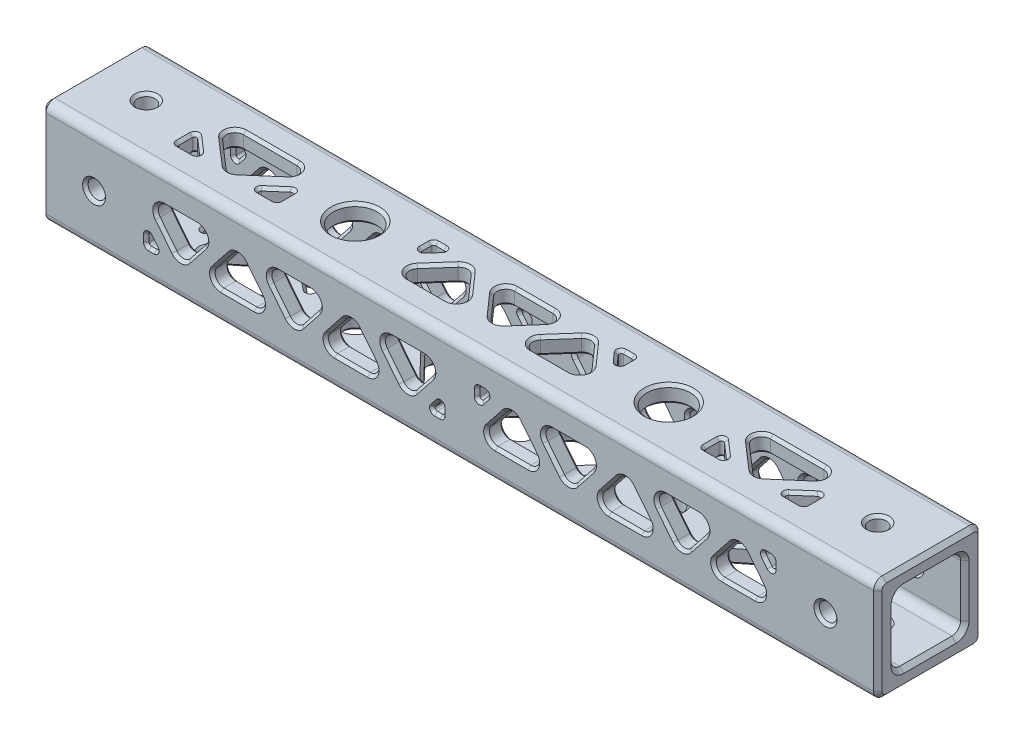
SolidWorks part; units mm, degrees
ref_plane "Front Plane" through (0, 0, 0) normal (0, 0, 1) x (1, 0, 0)
ref_plane "Top Plane" through (0, 0, 0) normal (0, 1, 0) x (1, 0, 0)
ref_plane "Right Plane" through (0, 0, 0) normal (1, 0, 0) x (0, 0, -1)
sketch "Sketch1" plane through (0, 0, 0) normal (1, 0, 0) x (0, 0, -1)
  line L1 (-6.35, -6.35) -> (6.35, -6.35)
  line L2 (-6.35, -6.35) -> (-6.35, 6.35)
  line L3 (-6.35, 6.35) -> (6.35, 6.35)
  line L4 (6.35, -6.35) -> (6.35, 6.35)
  line L5 (-6.35, -6.35) -> (6.35, 6.35) construction
  line L6 (-6.35, 6.35) -> (6.35, -6.35) construction
  line L7 (-9.525, -9.525) -> (9.525, -9.525)
  line L8 (-9.525, -9.525) -> (-9.525, 9.525)
  line L9 (-9.525, 9.525) -> (9.525, 9.525)
  line L10 (9.525, -9.525) -> (9.525, 9.525)
  line L11 (-9.525, -9.525) -> (9.525, 9.525) construction
  line L12 (-9.525, 9.525) -> (9.525, -9.525) construction
  point P0 (0, 0)
  point P6 (0, 0)
  dimension "D1" = 19.05
  dimension "D2" = 12.7
extrude "Boss-Extrude1" add sketch "Sketch1" along normal mid plane 152.4 contours L9 L10 L7 L8
hole_wizard "1/8 (0.125) Diameter Hole1" positions "Sketch2" profile "Sketch3" hole size "1/8" standard "ANSI Inch" end condition through all
sketch "Sketch2" plane through (0, 0, 9.525) normal (0, 0, 1) x (1, 0, 0)
  line L0 (-76.2, 0) -> (-66.675, 0) construction
  line L1 (-76.2, 9.525) -> (-76.2, -9.525) construction
  line L2 (-66.675, 0) -> (66.675, 0) construction
  line L3 (66.675, 0) -> (76.2, 0) construction
  line L4 (76.2, 9.525) -> (76.2, -9.525) construction
  point P35 (-66.675, 0)
  point P37 (66.675, 0)
  dimension "D1" = 9.525
sketch "Sketch3" plane through (-66.675, 0, 9.525) normal (1, 0, 0) x (0, -1, 0)
  line L0 (0, 0) -> (0, 19.05)
  line L1 (0, 19.05) -> (1.5875, 19.05)
  line L2 (1.5875, 19.05) -> (1.5875, 0)
  line L5 (1.5875, 0) -> (0, 0)
  line L11 (0, -6.35) -> (0, 107.95) construction
  dimension "Thru Hole Dia." = 3.175
  dimension "Thru Hole Depth" = 19.05
hole_wizard "1/8 (0.125) Diameter Hole2" positions "Sketch4" profile "Sketch5" hole size "1/8" standard "ANSI Inch" end condition through all
sketch "Sketch4" plane through (0, 9.525, 0) normal (0, 1, 0) x (1, 0, 0)
  line L0 (-76.2, 0) -> (-66.675, 0) construction
  line L1 (-76.2, 9.525) -> (-76.2, -9.525) construction
  line L2 (-66.675, 0) -> (66.675, 0) construction
  line L3 (66.675, 0) -> (76.2, 0) construction
  line L4 (76.2, 9.525) -> (76.2, -9.525) construction
  point P27 (-66.675, 0)
  point P29 (66.675, 0)
  dimension "D1" = 9.525
sketch "Sketch5" plane through (-66.675, 9.525, 0) normal (1, 0, 0) x (0, 0, 1)
  line L0 (0, 0) -> (0, 19.05)
  line L1 (0, 19.05) -> (1.5875, 19.05)
  line L2 (1.5875, 19.05) -> (1.5875, 0)
  line L5 (1.5875, 0) -> (0, 0)
  line L11 (0, -6.35) -> (0, 107.95) construction
  dimension "Thru Hole Dia." = 3.175
  dimension "Thru Hole Depth" = 19.05
hole_wizard "3/16 (0.1875) Diameter Hole1" positions "Sketch6" profile "Sketch7" hole size "3/16" standard "ANSI Inch" end condition up to next
sketch "Sketch6" plane through (0, -9.525, 0) normal (0, -1, 0) x (-1, 0, 0)
  line L0 (-28.575, 0) -> (28.575, 0) construction
  point P0 (28.575, 0)
  point P2 (-28.575, 0)
  dimension "D1" = 57.15
sketch "Sketch7" plane through (-28.575, -9.525, 0) normal (1, 0, 0) x (0, 0, -1)
  line L0 (0, 0) -> (0, 3.175)
  line L1 (0, 3.175) -> (2.3812, 3.175)
  line L2 (2.3812, 3.175) -> (2.3812, 0)
  line L5 (2.3812, 0) -> (0, 0)
  line L11 (0, -6.35) -> (0, 107.95) construction
  dimension "Thru Hole Dia." = 4.7625
  dimension "Thru Hole Depth" = 3.175
sketch "Sketch10" plane through (0, 9.525, 0) normal (0, 1, 0) x (1, 0, 0)
  line L0 (28.575, 0) -> (-28.575, 0) construction
  circle A0 centre (-28.575, 0) radius 3.9688
  circle A1 centre (28.575, 0) radius 3.9687
  circle A3 centre (28.575, 0) radius 2.3812 construction
  dimension "D1" = 7.9375
extrude "Cut-Extrude3" cut sketch "Sketch10" against normal up to next
ref_axis "Axis1" through (-82.0738, 0, 0) along (1, 0, 0)
sketch "Sketch9" plane through (0, -9.525, 0) normal (0, -1, 0) x (1, 0, 0)
  line L0 (-57.15, 9.525) -> (-57.15, -9.525) construction
  line L1 (76.2, 9.525) -> (-76.2, 9.525) construction
  line L2 (76.2, -9.525) -> (-76.2, -9.525) construction
  line L3 (57.15, 9.525) -> (57.15, -9.525) construction
  line L4 (-76.2, 9.525) -> (-76.2, -9.525) construction
  line L5 (-28.575, 0) -> (-28.575, -9.525) construction
  line L6 (-28.575, 0) -> (-28.575, 9.525) construction
  line L7 (-30.9562, 0) -> (-30.9563, -9.525) construction
  line L8 (-30.9562, 0) -> (-30.9563, 9.525) construction
  line L9 (-37.3062, 9.525) -> (-37.3062, -9.525) construction
  line L10 (-26.1938, 0) -> (-26.1938, -9.525) construction
  line L11 (-26.1938, 0) -> (-26.1938, 9.525) construction
  line L12 (-19.8438, 9.525) -> (-19.8438, -9.525) construction
  line L13 (-30.9562, 0) -> (-37.3062, 0) construction
  line L14 (-26.1938, 0) -> (-19.8438, 0) construction
  line L15 (28.575, 0) -> (28.575, 9.525) construction
  line L16 (28.575, 0) -> (28.575, -9.525) construction
  line L17 (30.9562, 0) -> (30.9562, -9.525) construction
  line L18 (30.9562, 0) -> (30.9562, 9.525) construction
  line L19 (26.1938, 0) -> (26.1938, -9.525) construction
  line L20 (26.1938, 0) -> (26.1938, 9.525) construction
  line L21 (19.8438, 9.525) -> (19.8438, -9.525) construction
  line L22 (19.8438, 0) -> (26.1938, 0) construction
  line L23 (37.3062, 9.525) -> (37.3062, -9.525) construction
  line L24 (30.9562, 0) -> (37.3062, 0) construction
  line L25 (57.15, 0) -> (76.2, 0) construction
  line L26 (76.2, 9.525) -> (76.2, -9.525) construction
  line L27 (-57.15, 0) -> (-76.2, 0) construction
  line L28 (-57.15, 3.9688) -> (-37.3062, 3.9688) construction
  line L29 (-57.15, -3.9688) -> (-37.3062, -3.9688) construction
  line L30 (-47.2281, -9.525) -> (-47.2281, -3.9688) construction
  line L31 (-47.2281, 3.9688) -> (-47.2281, 9.525) construction
  line L32 (-19.8438, 3.9688) -> (19.8438, 3.9688) construction
  line L33 (-19.8438, -3.9688) -> (19.8438, -3.9688) construction
  line L34 (37.3062, 3.9688) -> (57.15, 3.9688) construction
  line L35 (37.3062, -3.9688) -> (57.15, -3.9688) construction
  line L36 (-19.8438, 3.9688) -> (-19.8438, 0.5884)
  line L37 (-19.8438, 0.5884) -> (-16.5608, 3.9688)
  line L38 (-16.5608, 3.9688) -> (-19.8438, 3.9688)
  line L39 (-19.8438, -3.9688) -> (-12.1348, 3.9688)
  line L40 (-12.1348, 3.9688) -> (-4.4259, -3.9688)
  line L41 (-4.4259, -3.9688) -> (-19.8438, -3.9688)
  line L42 (-18.2023, 2.2786) -> (-15.9246, 0.0666) construction
  line L43 (-7.7089, 3.9688) -> (0, -3.9688)
  line L44 (0, -3.9688) -> (7.7089, 3.9688)
  line L45 (7.7089, 3.9688) -> (-7.7089, 3.9688)
  line L46 (19.8438, -3.9688) -> (12.1348, 3.9688)
  line L47 (12.1348, 3.9688) -> (4.4259, -3.9688)
  line L48 (4.4259, -3.9688) -> (19.8438, -3.9688)
  line L49 (16.5608, 3.9688) -> (19.8438, 3.9688)
  line L50 (19.8438, 3.9688) -> (19.8438, 0.5884)
  line L51 (19.8438, 0.5884) -> (16.5608, 3.9688)
  line L52 (-3.8545, 0) -> (-6.1321, -2.212) construction
  line L53 (3.8545, 0) -> (6.1321, -2.212) construction
  line L54 (18.2023, 2.2786) -> (15.9246, 0.0666) construction
  line L55 (-37.3062, -3.9688) -> (-37.3062, -0.0972)
  line L56 (-37.3062, -0.0972) -> (-42.1456, -3.9688)
  line L57 (-42.1456, -3.9688) -> (-37.3062, -3.9688)
  line L58 (-57.15, -3.9688) -> (-57.15, -0.0972)
  line L59 (-57.15, -0.0972) -> (-52.3106, -3.9688)
  line L60 (-52.3106, -3.9688) -> (-57.15, -3.9688)
  line L61 (-57.15, 3.9688) -> (-47.2281, -3.9688)
  line L62 (-47.2281, -3.9688) -> (-37.3062, 3.9688)
  line L63 (-37.3062, 3.9688) -> (-57.15, 3.9688)
  line L64 (-54.7303, -2.033) -> (-52.7469, 0.4463) construction
  line L65 (-39.7259, -2.033) -> (-41.7094, 0.4463) construction
  line L66 (37.3062, -0.0972) -> (37.3062, -3.9688)
  line L67 (37.3062, -3.9688) -> (42.1456, -3.9688)
  line L68 (42.1456, -3.9688) -> (37.3062, -0.0972)
  line L69 (52.3106, -3.9688) -> (57.15, -3.9688)
  line L70 (57.15, -3.9688) -> (57.15, -0.0972)
  line L71 (57.15, -0.0972) -> (52.3106, -3.9688)
  line L72 (37.3062, 3.9688) -> (47.2281, -3.9688)
  line L73 (47.2281, -3.9688) -> (57.15, 3.9688)
  line L74 (57.15, 3.9688) -> (37.3062, 3.9688)
  line L75 (39.7259, -2.033) -> (41.7094, 0.4463) construction
  line L76 (54.7303, -2.033) -> (52.7469, 0.4463) construction
  circle A0 centre (-28.575, 0) radius 2.3812 construction
  circle A1 centre (28.575, 0) radius 2.3812 construction
  dimension "D1" = 19.05
  dimension "D2" = 6.35
  dimension "D3" = 7.9375
  dimension "D4" = 3.175
extrude "Cut-Extrude2" cut sketch "Sketch9" against normal up to next contours L62 L63 L61
sketch "Sketch11" plane through (0, 9.525, 0) normal (0, 1, 0) x (1, 0, 0)
  line L0 (-57.15, 9.525) -> (-57.15, -9.525) construction
  line L1 (76.2, 9.525) -> (-76.2, 9.525) construction
  line L2 (76.2, -9.525) -> (-76.2, -9.525) construction
  line L3 (-76.2, 9.525) -> (-76.2, -9.525) construction
  line L4 (57.15, 9.525) -> (57.15, -9.525) construction
  line L5 (57.15, 0) -> (76.2, 0) construction
  line L6 (76.2, 9.525) -> (76.2, -9.525) construction
  line L7 (-57.15, 0) -> (-76.2, 0) construction
  line L8 (-28.575, 0) -> (-28.575, -9.525) construction
  line L9 (-28.575, 0) -> (-28.575, 9.525) construction
  line L10 (28.575, 0) -> (28.575, -9.525) construction
  line L11 (28.575, 0) -> (28.575, 9.525) construction
  line L12 (-32.5437, 0) -> (-32.5437, 9.525) construction
  line L13 (-32.5437, 0) -> (-32.5437, -9.525) construction
  line L14 (-24.6062, 0) -> (-24.6062, 9.525) construction
  line L15 (-24.6062, 0) -> (-24.6062, -9.525) construction
  line L16 (24.6062, 0) -> (24.6062, 9.525) construction
  line L17 (24.6062, 0) -> (24.6062, -9.525) construction
  line L18 (32.5437, 0) -> (32.5437, 9.525) construction
  line L19 (32.5437, 0) -> (32.5437, -9.525) construction
  line L20 (-38.8938, 9.525) -> (-38.8938, -9.525) construction
  line L21 (-18.2562, 9.525) -> (-18.2563, -9.525) construction
  line L22 (18.2562, 9.525) -> (18.2563, -9.525) construction
  line L23 (38.8938, 9.525) -> (38.8938, -9.525) construction
  line L24 (-32.5437, 0) -> (-38.8938, 0) construction
  line L25 (-24.6062, 0) -> (-18.2562, 0) construction
  line L26 (24.6062, 0) -> (18.2562, 0) construction
  line L27 (32.5437, 0) -> (38.8937, 0) construction
  line L28 (-57.15, 3.9688) -> (-38.8938, 3.9688) construction
  line L29 (-18.2562, 3.9688) -> (18.2562, 3.9688) construction
  line L30 (38.8937, 3.9688) -> (57.15, 3.9688) construction
  line L31 (57.15, -3.9688) -> (38.8937, -3.9688) construction
  line L32 (18.2562, -3.9688) -> (-18.2562, -3.9688) construction
  line L33 (-38.8938, -3.9688) -> (-57.15, -3.9688) construction
  line L34 (0, -3.9687) -> (0, -9.525) construction
  line L35 (0, 3.9687) -> (0, 9.525) construction
  line L36 (-57.15, -3.9688) -> (-57.15, -0.2387)
  line L37 (-57.15, -0.2387) -> (-52.8605, -3.9688)
  line L38 (-52.8605, -3.9688) -> (-57.15, -3.9688)
  line L39 (-57.15, 3.9688) -> (-48.0219, -3.9688)
  line L40 (-48.0219, -3.9688) -> (-38.8938, 3.9688)
  line L41 (-38.8938, 3.9688) -> (-57.15, 3.9688)
  line L42 (-43.1833, -3.9688) -> (-38.8938, -3.9688)
  line L43 (-38.8938, -3.9688) -> (-38.8938, -0.2387)
  line L44 (-38.8938, -0.2387) -> (-43.1833, -3.9688)
  line L45 (-55.0052, -2.1037) -> (-52.9219, 0.2921) construction
  line L46 (-41.0385, -2.1037) -> (-43.1219, 0.2921) construction
  line L47 (-18.2562, 3.9688) -> (-18.2562, 0.8276)
  line L48 (-18.2562, 0.8276) -> (-15.4821, 3.9688)
  line L49 (-15.4821, 3.9688) -> (-18.2562, 3.9688)
  line L50 (15.4821, 3.9688) -> (18.2562, 3.9688)
  line L51 (18.2562, 3.9688) -> (18.2562, 0.8276)
  line L52 (18.2562, 0.8276) -> (15.4821, 3.9688)
  line L53 (-18.2562, -3.9688) -> (-11.2461, 3.9688)
  line L54 (-11.2461, 3.9688) -> (-4.236, -3.9688)
  line L55 (-4.236, -3.9688) -> (-18.2562, -3.9688)
  line L56 (-7.0101, 3.9688) -> (0, -3.9687)
  line L57 (0, -3.9687) -> (7.0101, 3.9688)
  line L58 (7.0101, 3.9688) -> (-7.0101, 3.9688)
  line L59 (18.2562, -3.9688) -> (11.2461, 3.9688)
  line L60 (11.2461, 3.9688) -> (4.236, -3.9688)
  line L61 (4.236, -3.9688) -> (18.2562, -3.9688)
  line L62 (-16.8692, 2.3982) -> (-14.4894, 0.2964) construction
  line L63 (16.8692, 2.3982) -> (14.4894, 0.2964) construction
  line L64 (-3.5051, 0) -> (-5.8848, -2.1017) construction
  line L65 (3.5051, 0) -> (5.8848, -2.1017) construction
  line L66 (38.8937, -0.2387) -> (38.8937, -3.9688)
  line L67 (38.8937, -3.9688) -> (43.1833, -3.9688)
  line L68 (43.1833, -3.9688) -> (38.8937, -0.2387)
  line L69 (52.8605, -3.9688) -> (57.15, -3.9688)
  line L70 (57.15, -3.9688) -> (57.15, -0.2387)
  line L71 (57.15, -0.2387) -> (52.8605, -3.9688)
  line L72 (38.8937, 3.9688) -> (48.0219, -3.9688)
  line L73 (48.0219, -3.9688) -> (57.15, 3.9688)
  line L74 (57.15, 3.9688) -> (38.8937, 3.9688)
  line L75 (41.0385, -2.1037) -> (43.1219, 0.2921) construction
  line L76 (55.0052, -2.1037) -> (52.9219, 0.2921) construction
  circle A0 centre (-28.575, 0) radius 3.9688 construction
  circle A1 centre (28.575, 0) radius 3.9687 construction
  dimension "D1" = 19.05
  dimension "D2" = 6.35
  dimension "D3" = 7.9375
  dimension "D4" = 3.175
extrude "Cut-Extrude4" cut sketch "Sketch11" against normal up to next contours L39 L40 L41
sketch "Sketch13" plane through (0, 0, 9.525) normal (0, 0, 1) x (1, 0, 0)
  line L0 (-57.15, 9.525) -> (-57.15, -9.525) construction
  line L1 (76.2, 9.525) -> (-76.2, 9.525) construction
  line L2 (76.2, -9.525) -> (-76.2, -9.525) construction
  line L3 (57.15, 9.525) -> (57.15, -9.525) construction
  line L4 (-3.175, 9.525) -> (-3.175, -9.525) construction
  line L5 (3.175, 9.525) -> (3.175, -9.525) construction
  line L6 (-3.175, 0) -> (3.175, 0) construction
  line L7 (-57.15, 0) -> (-76.2, 0) construction
  line L9 (57.15, 0) -> (76.2, 0) construction
  line L10 (76.2, 9.525) -> (76.2, -9.525) construction
  line L11 (-57.15, 3.9688) -> (-3.175, 3.9688) construction
  line L12 (-57.15, -3.9688) -> (-3.175, -3.9688) construction
  line L13 (3.175, -3.9688) -> (57.15, -3.9688) construction
  line L14 (3.175, 3.9688) -> (57.15, 3.9688) construction
  line L15 (-30.1625, -3.9688) -> (-30.1625, -9.525) construction
  line L16 (-30.1625, 3.9688) -> (-30.1625, 9.525) construction
  line L17 (-57.15, -1.1411) -> (-57.15, -3.9688)
  line L18 (-57.15, -3.9688) -> (-54.9077, -3.9688)
  line L19 (-54.9077, -3.9688) -> (-57.15, -1.1411)
  line L20 (-3.175, -3.9688) -> (-3.175, -1.1411)
  line L21 (-3.175, -1.1411) -> (-5.4173, -3.9688)
  line L22 (-5.4173, -3.9688) -> (-3.175, -3.9688)
  line L23 (-30.1625, -3.9688) -> (-36.4569, 3.9688)
  line L24 (-36.4569, 3.9688) -> (-23.8681, 3.9688)
  line L25 (-23.8681, 3.9688) -> (-30.1625, -3.9688)
  line L26 (-57.15, 3.9688) -> (-50.8556, -3.9688)
  line L27 (-50.8556, -3.9688) -> (-44.5612, 3.9688)
  line L28 (-44.5612, 3.9688) -> (-57.15, 3.9688)
  line L29 (-3.175, 3.9688) -> (-9.4694, -3.9688)
  line L30 (-9.4694, -3.9688) -> (-15.7638, 3.9688)
  line L31 (-15.7638, 3.9688) -> (-3.175, 3.9688)
  line L32 (-46.8035, -3.9688) -> (-40.509, 3.9688)
  line L33 (-40.509, 3.9688) -> (-34.2146, -3.9688)
  line L34 (-34.2146, -3.9688) -> (-46.8035, -3.9688)
  line L35 (-26.1104, -3.9688) -> (-19.816, 3.9688)
  line L36 (-19.816, 3.9688) -> (-13.5215, -3.9688)
  line L37 (-13.5215, -3.9688) -> (-26.1104, -3.9688)
  line L38 (-56.0289, -2.5549) -> (-53.5411, -0.5822) construction
  line L39 (-47.7084, 0) -> (-45.2206, -1.9728) construction
  line L40 (-37.3618, 0) -> (-34.8741, 1.9728) construction
  line L41 (-22.9632, 0) -> (-25.4509, 1.9728) construction
  line L42 (-16.6687, 0) -> (-14.181, 1.9728) construction
  line L43 (-4.2961, -2.5549) -> (-6.7839, -0.5822) construction
  line L44 (3.175, 3.9688) -> (3.175, 1.1411)
  line L45 (3.175, 1.1411) -> (5.4173, 3.9688)
  line L46 (5.4173, 3.9688) -> (3.175, 3.9688)
  line L47 (57.15, 3.9688) -> (57.15, 1.1411)
  line L48 (57.15, 1.1411) -> (54.9077, 3.9688)
  line L49 (54.9077, 3.9688) -> (57.15, 3.9688)
  line L50 (23.8681, -3.9688) -> (30.1625, 3.9688)
  line L51 (30.1625, 3.9688) -> (36.4569, -3.9688)
  line L52 (36.4569, -3.9688) -> (23.8681, -3.9688)
  line L53 (3.175, -3.9688) -> (9.4694, 3.9688)
  line L54 (9.4694, 3.9688) -> (15.7638, -3.9688)
  line L55 (15.7638, -3.9688) -> (3.175, -3.9688)
  line L56 (13.5215, 3.9688) -> (19.816, -3.9688)
  line L57 (19.816, -3.9688) -> (26.1104, 3.9688)
  line L58 (26.1104, 3.9688) -> (13.5215, 3.9688)
  line L59 (57.15, -3.9688) -> (50.8556, 3.9688)
  line L60 (50.8556, 3.9688) -> (44.5612, -3.9688)
  line L61 (44.5612, -3.9688) -> (57.15, -3.9688)
  line L62 (34.2146, 3.9688) -> (40.509, -3.9688)
  line L63 (40.509, -3.9688) -> (46.8035, 3.9688)
  line L64 (46.8035, 3.9688) -> (34.2146, 3.9688)
  line L65 (4.2961, 2.5549) -> (6.7839, 0.5822) construction
  line L66 (16.6687, 0) -> (14.181, -1.9728) construction
  line L67 (22.9632, 0) -> (25.4509, -1.9728) construction
  line L68 (56.0289, 2.5549) -> (53.5411, 0.5822) construction
  line L69 (37.3618, 0) -> (34.8741, -1.9728) construction
  line L70 (43.6563, 0) -> (46.144, -1.9728) construction
  line L71 (-76.2, 9.525) -> (-76.2, -9.525) construction
  dimension "D1" = 19.05
  dimension "D2" = 6.35
  dimension "D3" = 7.9375
  dimension "D4" = 3.175
extrude "Cut-Extrude5" cut sketch "Sketch13" against normal up to next (3.175 mm away)
pattern_circular "CirPattern2" count 4 over 360 about axis through (-82.0738, 0, 0) along (1, 0, 0) skipping 1, 3 of "Cut-Extrude5"
fillet "Fillet1" radius 1.5875 98 edges at (0, 6.35, -6.35) (0, -6.35, -6.35) (0, -6.35, 6.35) (0, 6.35, 6.35) (0, -9.525, -9.525) (0, -9.525, 9.525) (0, 9.525, -9.525) (0, 9.525, 9.525) (50.8556, -3.9687, -7.9375) (57.15, 3.9688, -7.9375) (44.5612, 3.9688, -7.9375) (46.8035, -3.9687, -7.9375) (34.2146, -3.9688, -7.9375) (40.509, 3.9687, -7.9375) (30.1625, -3.9688, -7.9375) (36.4569, 3.9687, -7.9375) (23.8681, 3.9688, -7.9375) (26.1104, -3.9687, -7.9375) (13.5215, -3.9688, -7.9375) (19.816, 3.9688, -7.9375) (9.4694, -3.9687, -7.9375) (15.7638, 3.9688, -7.9375) (3.175, 3.9688, -7.9375) (-3.175, -3.9688, -7.9375) (-15.7638, -3.9688, -7.9375) (-9.4694, 3.9688, -7.9375) (-19.816, -3.9688, -7.9375) (-13.5215, 3.9687, -7.9375) (-26.1104, 3.9688, -7.9375) (-23.8681, -3.9688, -7.9375) (-36.4569, -3.9688, -7.9375) (-30.1625, 3.9688, -7.9375) (-40.509, -3.9688, -7.9375) (-34.2146, 3.9687, -7.9375) (-46.8035, 3.9688, -7.9375) (-44.5612, -3.9688, -7.9375) (-57.15, -3.9688, -7.9375) (-50.8556, 3.9688, -7.9375) (57.15, -7.9375, 3.9688) (47.2281, -7.9375, -3.9688) (37.3062, -7.9375, 3.9688) (19.8438, -7.9375, -3.9688) (4.4259, -7.9375, -3.9688) (12.1348, -7.9375, 3.9688) (-7.7089, -7.9375, 3.9688) (7.7089, -7.9375, 3.9688) (0, -7.9375, -3.9688) (-4.4259, -7.9375, -3.9688) (-19.8438, -7.9375, -3.9688) (-12.1348, -7.9375, 3.9688) (-57.15, -7.9375, 3.9688) (-47.2281, -7.9375, -3.9688) (-37.3062, -7.9375, 3.9688) (57.15, -3.9688, 7.9375) (50.8556, 3.9688, 7.9375) (44.5612, -3.9688, 7.9375) (34.2146, 3.9688, 7.9375) (46.8035, 3.9688, 7.9375) (40.509, -3.9688, 7.9375) (36.4569, -3.9688, 7.9375) (30.1625, 3.9688, 7.9375) (23.8681, -3.9688, 7.9375) (13.5215, 3.9688, 7.9375) (26.1104, 3.9688, 7.9375) (19.816, -3.9688, 7.9375) (15.7638, -3.9688, 7.9375) (9.4694, 3.9688, 7.9375) (3.175, -3.9688, 7.9375) (-15.7638, 3.9688, 7.9375) (-3.175, 3.9688, 7.9375) (-9.4694, -3.9688, 7.9375) (-13.5215, -3.9688, 7.9375) (-19.816, 3.9688, 7.9375) (-26.1104, -3.9688, 7.9375) (-23.8681, 3.9688, 7.9375) (-30.1625, -3.9688, 7.9375) (-36.4569, 3.9688, 7.9375) (-34.2146, -3.9688, 7.9375) (-46.8035, -3.9688, 7.9375) (-40.509, 3.9688, 7.9375) (-57.15, 3.9688, 7.9375) (-50.8556, -3.9688, 7.9375) (-44.5612, 3.9688, 7.9375) (57.15, 7.9375, -3.9688) (38.8937, 7.9375, -3.9687) (48.0219, 7.9375, 3.9688) (11.2461, 7.9375, -3.9688) (18.2563, 7.9375, 3.9688) (4.236, 7.9375, 3.9688) (7.0101, 7.9375, -3.9688) (-7.0101, 7.9375, -3.9688) (0, 7.9375, 3.9687) (-18.2562, 7.9375, 3.9688) (-4.236, 7.9375, 3.9688) (-11.2461, 7.9375, -3.9688) (-38.8938, 7.9375, -3.9688) (-57.15, 7.9375, -3.9687) (-48.0219, 7.9375, 3.9688)
fillet "Fillet2" radius 0.3969 60 edges at (57.15, -3.9688, -7.9375) (54.9077, -3.9688, -7.9375) (57.15, -1.1411, -7.9375) (5.4173, -3.9688, -7.9375) (3.175, -3.9688, -7.9375) (3.175, -1.1411, -7.9375) (-5.4173, 3.9688, -7.9375) (-3.175, 1.1411, -7.9375) (-3.175, 3.9688, -7.9375) (-57.15, 3.9688, -7.9375) (-57.15, 1.1411, -7.9375) (-54.9077, 3.9688, -7.9375) (18.2563, 7.9375, -3.9688) (18.2563, 7.9375, -0.8276) (15.4821, 7.9375, -3.9688) (-15.4821, 7.9375, -3.9688) (-18.2563, 7.9375, -0.8276) (-18.2563, 7.9375, -3.9688) (3.175, 3.9688, 7.9375) (3.175, 1.1411, 7.9375) (5.4173, 3.9688, 7.9375) (54.9077, 3.9688, 7.9375) (57.15, 1.1411, 7.9375) (57.15, 3.9688, 7.9375) (-3.175, -3.9688, 7.9375) (-3.175, -1.1411, 7.9375) (-5.4173, -3.9688, 7.9375) (-54.9077, -3.9688, 7.9375) (-57.15, -1.1411, 7.9375) (-57.15, -3.9688, 7.9375) (52.8605, 7.9375, 3.9687) (57.15, 7.9375, 0.2387) (57.15, 7.9375, 3.9688) (38.8937, 7.9375, 0.2387) (43.1833, 7.9375, 3.9688) (38.8937, 7.9375, 3.9688) (-43.1833, 7.9375, 3.9688) (-38.8938, 7.9375, 0.2387) (-38.8938, 7.9375, 3.9688) (-57.15, 7.9375, 0.2387) (-52.8605, 7.9375, 3.9688) (-57.15, 7.9375, 3.9688) (57.15, -7.9375, -0.0972) (52.3106, -7.9375, -3.9688) (57.15, -7.9375, -3.9688) (42.1456, -7.9375, -3.9688) (37.3062, -7.9375, -0.0972) (37.3062, -7.9375, -3.9688) (19.8438, -7.9375, 3.9688) (16.5608, -7.9375, 3.9688) (19.8438, -7.9375, 0.5884) (-19.8438, -7.9375, 3.9688) (-16.5608, -7.9375, 3.9688) (-19.8438, -7.9375, 0.5884) (-42.1456, -7.9375, -3.9688) (-37.3062, -7.9375, -0.0972) (-37.3062, -7.9375, -3.9688) (-52.3106, -7.9375, -3.9688) (-57.15, -7.9375, -0.0972) (-57.15, -7.9375, -3.9688)
chamfer "Chamfer2" distance 0.762 angle 45 32 edges at (-76.2, 5.885, 5.885) (-76.2, 6.35, 0) (-76.2, 5.885, -5.885) (-76.2, 0, -6.35) (-76.2, -5.885, -5.885) (-76.2, -6.35, 0) (-76.2, -5.885, 5.885) (-76.2, 0, 6.35) (-76.2, 9.06, -9.06) (-76.2, 9.525, 0) (-76.2, 9.06, 9.06) (-76.2, 0, 9.525) (-76.2, -9.06, 9.06) (-76.2, -9.525, 0) (-76.2, -9.06, -9.06) (-76.2, 0, -9.525) (76.2, 5.885, -5.885) (76.2, 6.35, 0) (76.2, 5.885, 5.885) (76.2, 0, 6.35) (76.2, -5.885, 5.885) (76.2, -6.35, 0) (76.2, -5.885, -5.885) (76.2, 0, -6.35) (76.2, -9.06, 9.06) (76.2, 0, 9.525) (76.2, 9.06, 9.06) (76.2, 9.525, 0) (76.2, 9.06, -9.06) (76.2, 0, -9.525) (76.2, -9.06, -9.06) (76.2, -9.525, 0)
chamfer "Chamfer3" distance 0.508 angle 45 624 edges at (56.241, -3.9688, -9.525) (56.241, -3.9688, -6.35) (57.15, -2.9261, -9.525) (57.15, -2.9261, -6.35) (55.9301, -2.6795, -9.525) (55.9301, -2.6795, -6.35) (4.084, -3.9688, -9.525) (4.084, -3.9688, -6.35) (4.3949, -2.6795, -9.525) (4.3949, -2.6795, -6.35) (3.175, -2.9261, -9.525) (3.175, -2.9261, -6.35) (-4.084, 3.9688, -9.525) (-4.084, 3.9688, -6.35) (-4.3949, 2.6795, -9.525) (-4.3949, 2.6795, -6.35) (-3.175, 2.9261, -9.525) (-3.175, 2.9261, -6.35) (-56.241, 3.9688, -9.525) (-56.241, 3.9688, -6.35) (-57.15, 2.9261, -9.525) (-57.15, 2.9261, -6.35) (-55.9301, 2.6795, -9.525) (-55.9301, 2.6795, -6.35) (17.1107, 9.525, -3.9688) (17.1107, 6.35, -3.9688) (18.2562, 9.525, -2.7242) (18.2562, 6.35, -2.7242) (16.8133, 9.525, -2.4615) (16.8133, 6.35, -2.4615) (-17.1107, 9.525, -3.9688) (-17.1107, 6.35, -3.9688) (-16.8133, 9.525, -2.4615) (-16.8133, 6.35, -2.4615) (-18.2562, 9.525, -2.7242) (-18.2562, 6.35, -2.7242) (3.175, 2.9261, 9.525) (3.175, 2.9261, 6.35) (4.084, 3.9688, 9.525) (4.084, 3.9688, 6.35) (4.3949, 2.6795, 9.525) (4.3949, 2.6795, 6.35) (55.9301, 2.6795, 9.525) (55.9301, 2.6795, 6.35) (56.241, 3.9688, 9.525) (56.241, 3.9688, 6.35) (57.15, 2.9261, 9.525) (57.15, 2.9261, 6.35) (-3.175, -2.9261, 9.525) (-3.175, -2.9261, 6.35) (-4.084, -3.9688, 9.525) (-4.084, -3.9688, 6.35) (-4.3949, -2.6795, 9.525) (-4.3949, -2.6795, 6.35) (-55.9301, -2.6795, 9.525) (-55.9301, -2.6795, 6.35) (-56.241, -3.9688, 9.525) (-56.241, -3.9688, 6.35) (-57.15, -2.9261, 9.525) (-57.15, -2.9261, 6.35) (55.3374, 9.525, 3.9688) (55.3374, 6.35, 3.9688) (55.077, 9.525, 2.0413) (55.077, 6.35, 2.0413) (57.15, 9.525, 2.3408) (57.15, 6.35, 2.3408) (38.8937, 9.525, 2.3408) (38.8937, 6.35, 2.3408) (40.9667, 9.525, 2.0413) (40.9667, 6.35, 2.0413) (40.7063, 9.525, 3.9688) (40.7063, 6.35, 3.9688) (-40.7063, 9.525, 3.9688) (-40.7063, 6.35, 3.9688) (-40.9667, 9.525, 2.0413) (-40.9667, 6.35, 2.0413) (-38.8938, 9.525, 2.3408) (-38.8938, 6.35, 2.3408) (-57.15, 9.525, 2.3408) (-57.15, 6.35, 2.3408) (-55.077, 9.525, 2.0413) (-55.077, 6.35, 2.0413) (-55.3374, 9.525, 3.9688) (-55.3374, 6.35, 3.9688) (54.8496, -9.525, -1.9375) (54.8496, -6.35, -1.9375) (57.15, -9.525, -2.2474) (57.15, -6.35, -2.2474) (55.0976, -9.525, -3.9688) (55.0976, -6.35, -3.9688) (39.6066, -9.525, -1.9375) (39.6066, -6.35, -1.9375) (39.3587, -9.525, -3.9688) (39.3587, -6.35, -3.9688) (37.3062, -9.525, -2.2474) (37.3062, -6.35, -2.2474) (18.4732, -9.525, 3.9688) (18.4732, -6.35, 3.9688) (19.8438, -9.525, 2.5693) (19.8438, -6.35, 2.5693) (18.1885, -9.525, 2.2928) (18.1885, -6.35, 2.2928) (-19.8438, -9.525, 2.5693) (-19.8438, -6.35, 2.5693) (-18.4732, -9.525, 3.9688) (-18.4732, -6.35, 3.9688) (-18.1885, -9.525, 2.2928) (-18.1885, -6.35, 2.2928) (-39.3587, -9.525, -3.9688) (-39.3587, -6.35, -3.9688) (-39.6066, -9.525, -1.9375) (-39.6066, -6.35, -1.9375) (-37.3062, -9.525, -2.2474) (-37.3062, -6.35, -2.2474) (-54.8496, -9.525, -1.9375) (-54.8496, -6.35, -1.9375) (-55.0976, -9.525, -3.9688) (-55.0976, -6.35, -3.9688) (-57.15, -9.525, -2.2474) (-57.15, -6.35, -2.2474) (57.0338, -3.8525, -9.525) (57.0338, -3.8525, -6.35) (55.3716, -3.7446, -9.525) (55.3716, -3.7446, -6.35) (56.8837, -1.9056, -9.525) (56.8837, -1.9056, -6.35) (4.9534, -3.7446, -9.525) (4.9534, -3.7446, -6.35) (3.2912, -3.8525, -9.525) (3.2912, -3.8525, -6.35) (3.4413, -1.9056, -9.525) (3.4413, -1.9056, -6.35) (-4.9534, 3.7446, -9.525) (-4.9534, 3.7446, -6.35) (-3.4413, 1.9056, -9.525) (-3.4413, 1.9056, -6.35) (-3.2912, 3.8525, -9.525) (-3.2912, 3.8525, -6.35) (-57.0338, 3.8525, -9.525) (-57.0338, 3.8525, -6.35) (-56.8837, 1.9056, -9.525) (-56.8837, 1.9056, -6.35) (-55.3716, 3.7446, -9.525) (-55.3716, 3.7446, -6.35) (18.14, 9.525, -3.8525) (18.14, 6.35, -3.8525) (17.9998, 9.525, -1.5053) (17.9998, 6.35, -1.5053) (16.0003, 9.525, -3.735) (16.0003, 6.35, -3.735) (-16.0003, 9.525, -3.735) (-16.0003, 6.35, -3.735) (-17.9998, 9.525, -1.5053) (-17.9998, 6.35, -1.5053) (-18.14, 9.525, -3.8525) (-18.14, 6.35, -3.8525) (3.2912, 3.8525, 9.525) (3.2912, 3.8525, 6.35) (3.4413, 1.9056, 9.525) (3.4413, 1.9056, 6.35) (4.9534, 3.7446, 9.525) (4.9534, 3.7446, 6.35) (55.3716, 3.7446, 9.525) (55.3716, 3.7446, 6.35) (56.8837, 1.9056, 9.525) (56.8837, 1.9056, 6.35) (57.0338, 3.8525, 9.525) (57.0338, 3.8525, 6.35) (-3.2912, -3.8525, 9.525) (-3.2912, -3.8525, 6.35) (-3.4413, -1.9056, 9.525) (-3.4413, -1.9056, 6.35) (-4.9534, -3.7446, 9.525) (-4.9534, -3.7446, 6.35) (-55.3716, -3.7446, 9.525) (-55.3716, -3.7446, 6.35) (-56.8837, -1.9056, 9.525) (-56.8837, -1.9056, 6.35) (-57.0338, -3.8525, 9.525) (-57.0338, -3.8525, 6.35) (53.55, 9.525, 3.7109) (53.55, 6.35, 3.7109) (56.9177, 9.525, 0.7486) (56.9177, 6.35, 0.7486) (57.0338, 9.525, 3.8525) (57.0338, 6.35, 3.8525) (39.1261, 9.525, 0.7486) (39.1261, 6.35, 0.7486) (42.4938, 9.525, 3.7109) (42.4938, 6.35, 3.7109) (39.01, 9.525, 3.8525) (39.01, 6.35, 3.8525) (-42.4938, 9.525, 3.7109) (-42.4938, 6.35, 3.7109) (-39.1261, 9.525, 0.7486) (-39.1261, 6.35, 0.7486) (-39.01, 9.525, 3.8525) (-39.01, 6.35, 3.8525) (-56.9177, 9.525, 0.7486) (-56.9177, 6.35, 0.7486) (-53.55, 9.525, 3.7109) (-53.55, 6.35, 3.7109) (-57.0338, 9.525, 3.8525) (-57.0338, 6.35, 3.8525) (56.925, -9.525, -0.5653) (56.925, -6.35, -0.5653) (53.0675, -9.525, -3.7032) (53.0675, -6.35, -3.7032) (57.0338, -9.525, -3.8525) (57.0338, -6.35, -3.8525) (41.3887, -9.525, -3.7032) (41.3887, -6.35, -3.7032) (37.5312, -9.525, -0.5653) (37.5312, -6.35, -0.5653) (37.4225, -9.525, -3.8525) (37.4225, -6.35, -3.8525) (19.7275, -9.525, 3.8525) (19.7275, -6.35, 3.8525) (17.1339, -9.525, 3.7264) (17.1339, -6.35, 3.7264) (19.5961, -9.525, 1.199) (19.5961, -6.35, 1.199) (-19.7275, -9.525, 3.8525) (-19.7275, -6.35, 3.8525) (-17.1339, -9.525, 3.7264) (-17.1339, -6.35, 3.7264) (-19.5961, -9.525, 1.199) (-19.5961, -6.35, 1.199) (-41.3887, -9.525, -3.7032) (-41.3887, -6.35, -3.7032) (-37.5312, -9.525, -0.5653) (-37.5312, -6.35, -0.5653) (-37.4225, -9.525, -3.8525) (-37.4225, -6.35, -3.8525) (-53.0675, -9.525, -3.7032) (-53.0675, -6.35, -3.7032) (-56.925, -9.525, -0.5653) (-56.925, -6.35, -0.5653) (-57.0338, -9.525, -3.8525) (-57.0338, -6.35, -3.8525) (65.0875, 0, 6.35) (68.2625, 0, -6.35) (68.2625, 0, -9.525) (68.2625, 0, 9.525) (-68.2625, 0, 6.35) (-65.0875, 0, -6.35) (-65.0875, 0, -9.525) (-65.0875, 0, 9.525) (66.675, -6.35, 1.5875) (66.675, 6.35, -1.5875) (66.675, 9.525, 1.5875) (66.675, -9.525, 1.5875) (-66.675, -6.35, 1.5875) (-66.675, 6.35, -1.5875) (-66.675, 9.525, 1.5875) (-66.675, -9.525, 1.5875) (48.107, -0.5027, -9.525) (48.107, -0.5027, -6.35) (53.6042, -0.5027, -9.525) (53.6042, -0.5027, -6.35) (50.8556, 3.9688, -9.525) (50.8556, 3.9688, -6.35) (40.509, -3.9688, -9.525) (40.509, -3.9688, -6.35) (43.2576, 0.5027, -9.525) (43.2576, 0.5027, -6.35) (37.7604, 0.5027, -9.525) (37.7604, 0.5027, -6.35) (27.4139, -0.5027, -9.525) (27.4139, -0.5027, -6.35) (32.9111, -0.5027, -9.525) (32.9111, -0.5027, -6.35) (30.1625, 3.9688, -9.525) (30.1625, 3.9688, -6.35) (19.816, -3.9688, -9.525) (19.816, -3.9688, -6.35) (22.5646, 0.5027, -9.525) (22.5646, 0.5027, -6.35) (17.0674, 0.5027, -9.525) (17.0674, 0.5027, -6.35) (6.7208, -0.5027, -9.525) (6.7208, -0.5027, -6.35) (12.218, -0.5027, -9.525) (12.218, -0.5027, -6.35) (9.4694, 3.9688, -9.525) (9.4694, 3.9688, -6.35) (-9.4694, -3.9688, -9.525) (-9.4694, -3.9688, -6.35) (-6.7208, 0.5027, -9.525) (-6.7208, 0.5027, -6.35) (-12.218, 0.5027, -9.525) (-12.218, 0.5027, -6.35) (28.575, -9.525, -2.3812) (28.575, -6.35, 2.3812) (-22.5646, -0.5027, -9.525) (-22.5646, -0.5027, -6.35) (-17.0674, -0.5027, -9.525) (-17.0674, -0.5027, -6.35) (-19.816, 3.9688, -9.525) (-19.816, 3.9688, -6.35) (-30.1625, -3.9688, -9.525) (-30.1625, -3.9688, -6.35) (-27.4139, 0.5027, -9.525) (-27.4139, 0.5027, -6.35) (-32.9111, 0.5027, -9.525) (-32.9111, 0.5027, -6.35) (-43.2576, -0.5027, -9.525) (-43.2576, -0.5027, -6.35) (-37.7604, -0.5027, -9.525) (-37.7604, -0.5027, -6.35) (-40.509, 3.9688, -9.525) (-40.509, 3.9688, -6.35) (-50.8556, -3.9688, -9.525) (-50.8556, -3.9688, -6.35) (-48.107, 0.5027, -9.525) (-48.107, 0.5027, -6.35) (-53.6042, 0.5027, -9.525) (-53.6042, 0.5027, -6.35) (47.2281, -9.525, 3.9688) (47.2281, -6.35, 3.9688) (50.918, -9.525, -1.0169) (50.918, -6.35, -1.0169) (43.5383, -9.525, -1.0169) (43.5383, -6.35, -1.0169) (15.2507, -9.525, 0.7605) (15.2507, -6.35, 0.7605) (12.1348, -9.525, -3.9688) (12.1348, -6.35, -3.9688) (9.019, -9.525, 0.7605) (9.019, -6.35, 0.7605) (-3.1159, -9.525, -0.7605) (-3.1159, -6.35, -0.7605) (0, -9.525, 3.9688) (0, -6.35, 3.9688) (3.1159, -9.525, -0.7605) (3.1159, -6.35, -0.7605) (-9.019, -9.525, 0.7605) (-9.019, -6.35, 0.7605) (-12.1348, -9.525, -3.9688) (-12.1348, -6.35, -3.9688) (-28.575, -9.525, -2.3812) (-15.2507, -9.525, 0.7605) (-15.2507, -6.35, 0.7605) (-28.575, -6.35, 2.3812) (-50.918, -9.525, -1.0169) (-50.918, -6.35, -1.0169) (-47.2281, -9.525, 3.9688) (-47.2281, -6.35, 3.9688) (-43.5383, -9.525, -1.0169) (-43.5383, -6.35, -1.0169) (53.6042, 0.5027, 9.525) (53.6042, 0.5027, 6.35) (50.8556, -3.9688, 9.525) (50.8556, -3.9688, 6.35) (48.107, 0.5027, 9.525) (48.107, 0.5027, 6.35) (37.7604, -0.5027, 9.525) (37.7604, -0.5027, 6.35) (40.509, 3.9688, 9.525) (40.509, 3.9688, 6.35) (43.2576, -0.5027, 9.525) (43.2576, -0.5027, 6.35) (32.9111, 0.5027, 9.525) (32.9111, 0.5027, 6.35) (30.1625, -3.9688, 9.525) (30.1625, -3.9688, 6.35) (27.4139, 0.5027, 9.525) (27.4139, 0.5027, 6.35) (17.0674, -0.5027, 9.525) (17.0674, -0.5027, 6.35) (19.816, 3.9688, 9.525) (19.816, 3.9688, 6.35) (22.5646, -0.5027, 9.525) (22.5646, -0.5027, 6.35) (12.218, 0.5027, 9.525) (12.218, 0.5027, 6.35) (9.4694, -3.9688, 9.525) (9.4694, -3.9688, 6.35) (6.7208, 0.5027, 9.525) (6.7208, 0.5027, 6.35) (-12.218, -0.5027, 9.525) (-12.218, -0.5027, 6.35) (-9.4694, 3.9688, 9.525) (-9.4694, 3.9688, 6.35) (-6.7208, -0.5027, 9.525) (-6.7208, -0.5027, 6.35) (-17.0674, 0.5027, 9.525) (-17.0674, 0.5027, 6.35) (-19.816, -3.9688, 9.525) (-19.816, -3.9688, 6.35) (-22.5646, 0.5027, 9.525) (-22.5646, 0.5027, 6.35) (-30.1625, 3.9688, 9.525) (-30.1625, 3.9688, 6.35) (-27.4139, -0.5027, 9.525) (-27.4139, -0.5027, 6.35) (-32.9111, -0.5027, 9.525) (-32.9111, -0.5027, 6.35) (-37.7604, 0.5027, 9.525) (-37.7604, 0.5027, 6.35) (-40.509, -3.9688, 9.525) (-40.509, -3.9688, 6.35) (-43.2576, 0.5027, 9.525) (-43.2576, 0.5027, 6.35) (-28.575, 6.35, -3.9688) (-53.6042, -0.5027, 9.525) (-53.6042, -0.5027, 6.35) (-28.575, 9.525, 3.9688) (-50.8556, 3.9688, 9.525) (-50.8556, 3.9688, 6.35) (-48.107, -0.5027, 9.525) (-48.107, -0.5027, 6.35) (48.0219, 9.525, -3.9688) (48.0219, 6.35, -3.9688) (51.5052, 9.525, 0.9398) (51.5052, 6.35, 0.9398) (44.5386, 9.525, 0.9398) (44.5386, 6.35, 0.9398) (8.3112, 9.525, -0.6455) (8.3112, 6.35, -0.6455) (14.1811, 9.525, -0.6455) (28.575, 6.35, -3.9687) (14.1811, 6.35, -0.6455) (28.575, 9.525, 3.9687) (11.2461, 9.525, 3.9688) (11.2461, 6.35, 3.9688) (0, 9.525, -3.9688) (0, 6.35, -3.9688) (2.935, 9.525, 0.6455) (2.935, 6.35, 0.6455) (-2.935, 9.525, 0.6455) (-2.935, 6.35, 0.6455) (-11.2461, 9.525, 3.9688) (-11.2461, 6.35, 3.9688) (-14.1811, 9.525, -0.6455) (-14.1811, 6.35, -0.6455) (-8.3112, 9.525, -0.6455) (-8.3112, 6.35, -0.6455) (-48.0219, 9.525, -3.9688) (-48.0219, 6.35, -3.9688) (-44.5386, 9.525, 0.9398) (-44.5386, 6.35, 0.9398) (-51.5052, 9.525, 0.9398) (-51.5052, 6.35, 0.9398) (50.8556, -3.0013, -9.525) (50.8556, -3.0013, -6.35) (55.2944, 3.072, -9.525) (55.2944, 3.072, -6.35) (46.4168, 3.072, -9.525) (46.4168, 3.072, -6.35) (44.9479, -3.072, -9.525) (44.9479, -3.072, -6.35) (36.0702, -3.072, -9.525) (36.0702, -3.072, -6.35) (40.509, 3.0013, -9.525) (40.509, 3.0013, -6.35) (30.1625, -3.0013, -9.525) (30.1625, -3.0013, -6.35) (34.6013, 3.072, -9.525) (34.6013, 3.072, -6.35) (25.7237, 3.072, -9.525) (25.7237, 3.072, -6.35) (24.2548, -3.072, -9.525) (24.2548, -3.072, -6.35) (15.3771, -3.072, -9.525) (15.3771, -3.072, -6.35) (19.816, 3.0013, -9.525) (19.816, 3.0013, -6.35) (9.4694, -3.0013, -9.525) (9.4694, -3.0013, -6.35) (13.9082, 3.072, -9.525) (13.9082, 3.072, -6.35) (5.0306, 3.072, -9.525) (5.0306, 3.072, -6.35) (-5.0306, -3.072, -9.525) (-5.0306, -3.072, -6.35) (-13.9082, -3.072, -9.525) (-13.9082, -3.072, -6.35) (-9.4694, 3.0013, -9.525) (-9.4694, 3.0013, -6.35) (-19.816, -3.0013, -9.525) (-19.816, -3.0013, -6.35) (-15.3771, 3.072, -9.525) (-15.3771, 3.072, -6.35) (-24.2548, 3.072, -9.525) (-24.2548, 3.072, -6.35) (-25.7237, -3.072, -9.525) (-25.7237, -3.072, -6.35) (-34.6013, -3.072, -9.525) (-34.6013, -3.072, -6.35) (-30.1625, 3.0013, -9.525) (-30.1625, 3.0013, -6.35) (-40.509, -3.0013, -9.525) (-40.509, -3.0013, -6.35) (-36.0702, 3.072, -9.525) (-36.0702, 3.072, -6.35) (-44.9479, 3.072, -9.525) (-44.9479, 3.072, -6.35) (-46.4168, -3.072, -9.525) (-46.4168, -3.072, -6.35) (-55.2944, -3.072, -9.525) (-55.2944, -3.072, -6.35) (-50.8556, 3.0013, -9.525) (-50.8556, 3.0013, -6.35) (54.1224, -9.525, 2.9067) (54.1224, -6.35, 2.9067) (47.2281, -9.525, -3.5233) (47.2281, -6.35, -3.5233) (40.3339, -9.525, 2.9067) (40.3339, -6.35, 2.9067) (17.5512, -9.525, -2.9995) (17.5512, -6.35, -2.9995) (6.7185, -9.525, -2.9995) (6.7185, -6.35, -2.9995) (12.1348, -9.525, 3.2777) (12.1348, -6.35, 3.2777) (-5.4163, -9.525, 2.9995) (-5.4163, -6.35, 2.9995) (5.4163, -9.525, 2.9995) (5.4163, -6.35, 2.9995) (0, -9.525, -3.2777) (0, -6.35, -3.2777) (-6.7185, -9.525, -2.9995) (-6.7185, -6.35, -2.9995) (-17.5512, -9.525, -2.9995) (-17.5512, -6.35, -2.9995) (-12.1348, -9.525, 3.2777) (-12.1348, -6.35, 3.2777) (-54.1224, -9.525, 2.9067) (-54.1224, -6.35, 2.9067) (-47.2281, -9.525, -3.5233) (-47.2281, -6.35, -3.5233) (-40.3339, -9.525, 2.9067) (-40.3339, -6.35, 2.9067) (55.2944, -3.072, 9.525) (55.2944, -3.072, 6.35) (50.8556, 3.0013, 9.525) (50.8556, 3.0013, 6.35) (46.4168, -3.072, 9.525) (46.4168, -3.072, 6.35) (36.0702, 3.072, 9.525) (36.0702, 3.072, 6.35) (44.9479, 3.072, 9.525) (44.9479, 3.072, 6.35) (40.509, -3.0013, 9.525) (40.509, -3.0013, 6.35) (34.6013, -3.072, 9.525) (34.6013, -3.072, 6.35) (30.1625, 3.0013, 9.525) (30.1625, 3.0013, 6.35) (25.7237, -3.072, 9.525) (25.7237, -3.072, 6.35) (15.3771, 3.072, 9.525) (15.3771, 3.072, 6.35) (24.2548, 3.072, 9.525) (24.2548, 3.072, 6.35) (19.816, -3.0013, 9.525) (19.816, -3.0013, 6.35) (13.9082, -3.072, 9.525) (13.9082, -3.072, 6.35) (9.4694, 3.0013, 9.525) (9.4694, 3.0013, 6.35) (5.0306, -3.072, 9.525) (5.0306, -3.072, 6.35) (-13.9082, 3.072, 9.525) (-13.9082, 3.072, 6.35) (-5.0306, 3.072, 9.525) (-5.0306, 3.072, 6.35) (-9.4694, -3.0013, 9.525) (-9.4694, -3.0013, 6.35) (-15.3771, -3.072, 9.525) (-15.3771, -3.072, 6.35) (-19.816, 3.0013, 9.525) (-19.816, 3.0013, 6.35) (-24.2548, -3.072, 9.525) (-24.2548, -3.072, 6.35) (-25.7237, 3.072, 9.525) (-25.7237, 3.072, 6.35) (-30.1625, -3.0013, 9.525) (-30.1625, -3.0013, 6.35) (-34.6013, 3.072, 9.525) (-34.6013, 3.072, 6.35) (-36.0702, -3.072, 9.525) (-36.0702, -3.072, 6.35) (-44.9479, -3.072, 9.525) (-44.9479, -3.072, 6.35) (-40.509, 3.0013, 9.525) (-40.509, 3.0013, 6.35) (-55.2944, 3.072, 9.525) (-55.2944, 3.072, 6.35) (-50.8556, -3.0013, 9.525) (-50.8556, -3.0013, 6.35) (-46.4168, 3.072, 9.525) (-46.4168, 3.072, 6.35) (54.392, 9.525, -2.9373) (54.392, 6.35, -2.9373) (41.6518, 9.525, -2.9373) (41.6518, 6.35, -2.9373) (48.0219, 9.525, 3.4525) (48.0219, 6.35, 3.4525) (11.2461, 9.525, -3.1581) (11.2461, 6.35, -3.1581) (16.1834, 9.525, 3.0339) (16.1834, 6.35, 3.0339) (6.3088, 9.525, 3.0339) (6.3088, 6.35, 3.0339) (4.9373, 9.525, -3.0339) (4.9373, 6.35, -3.0339) (-4.9373, 9.525, -3.0339) (-4.9373, 6.35, -3.0339) (0, 9.525, 3.1581) (0, 6.35, 3.1581) (-16.1834, 9.525, 3.0339) (-16.1834, 6.35, 3.0339) (-6.3088, 9.525, 3.0339) (-6.3088, 6.35, 3.0339) (-11.2461, 9.525, -3.1581) (-11.2461, 6.35, -3.1581) (-41.6518, 9.525, -2.9373) (-41.6518, 6.35, -2.9373) (-54.392, 9.525, -2.9373) (-54.392, 6.35, -2.9373) (-48.0219, 9.525, 3.4525) (-48.0219, 6.35, 3.4525)
